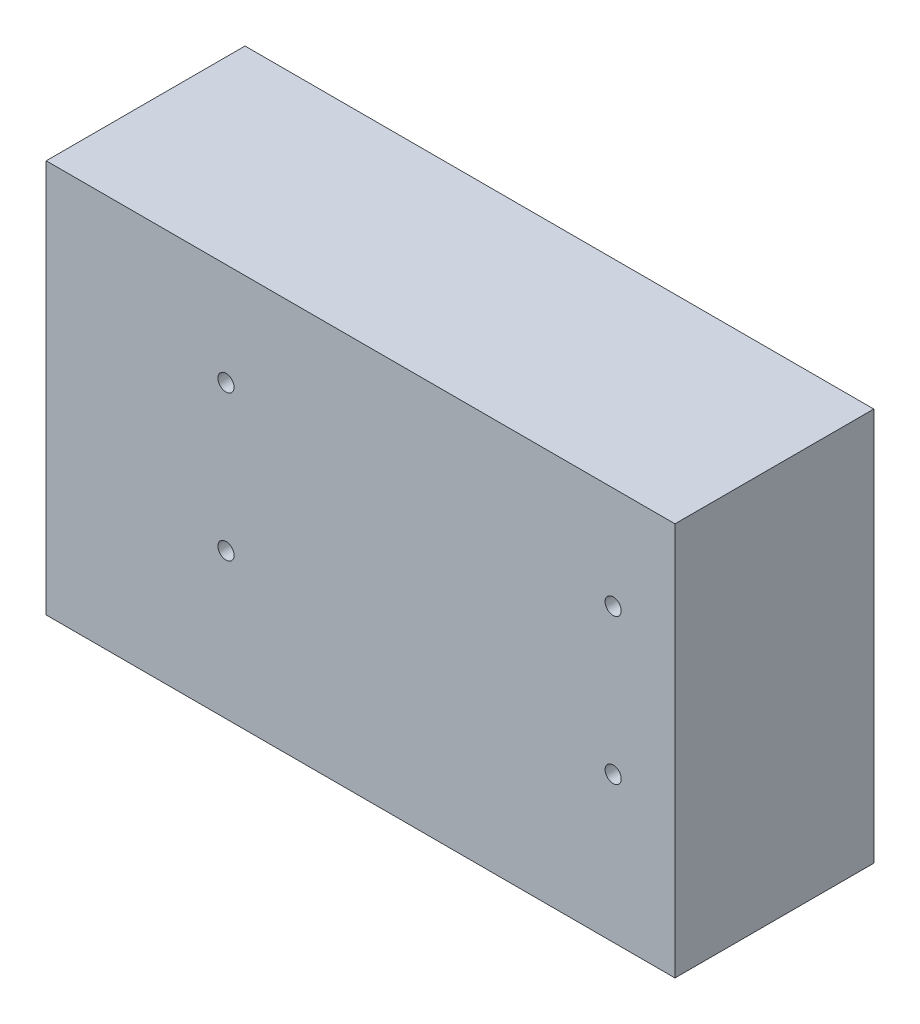
SolidWorks part; units mm, degrees
ref_plane "Ön Düzlem" through (0, 0, 0) normal (0, 0, 1) x (1, 0, 0)
ref_plane "Üst Düzlem" through (0, 0, 0) normal (0, 1, 0) x (1, 0, 0)
ref_plane "Sağ Düzlem" through (0, 0, 0) normal (1, 0, 0) x (0, 0, -1)
sketch "Sketch1" plane through (0, 0, 0) normal (0, 0, 1) x (1, 0, 0)
  line L1 (-33.05, 20.675) -> (33.05, 20.675)
  line L2 (-33.05, 20.675) -> (-33.05, -20.675)
  line L3 (-33.05, -20.675) -> (33.05, -20.675)
  line L4 (33.05, 20.675) -> (33.05, -20.675)
  line L5 (-33.05, 20.675) -> (33.05, -20.675) construction
  line L6 (-33.05, -20.675) -> (33.05, 20.675) construction
  point P0 (0, 0)
  dimension "D1" = 66.1
  dimension "D2" = 41.35
extrude "Boss-Extrude1" add sketch "Sketch1" along normal blind 20.9
sketch "Sketch2" plane through (0, 0, 0) normal (0, 0, -1) x (-1, 0, 0)
  line L0 (-33.05, 20.675) -> (33.05, 20.675) construction
  line L1 (-33.05, -20.675) -> (-33.05, 20.675) construction
  circle A0 centre (-26.55, 9.925) radius 0.85
  circle A2 centre (-26.55, -5.375) radius 0.85
  circle A3 centre (14.15, 9.925) radius 0.85
  circle A4 centre (14.15, -5.375) radius 0.85
  dimension "D1" = 1.7
  dimension "D2" = 1.7
  dimension "D3" = 10.75
  dimension "D4" = 6.5
  dimension "D5" = 15.3
  dimension "D6" = 15.3
  dimension "D7" = 40.7
extrude "Cut-Extrude1" cut sketch "Sketch2" against normal blind 30
